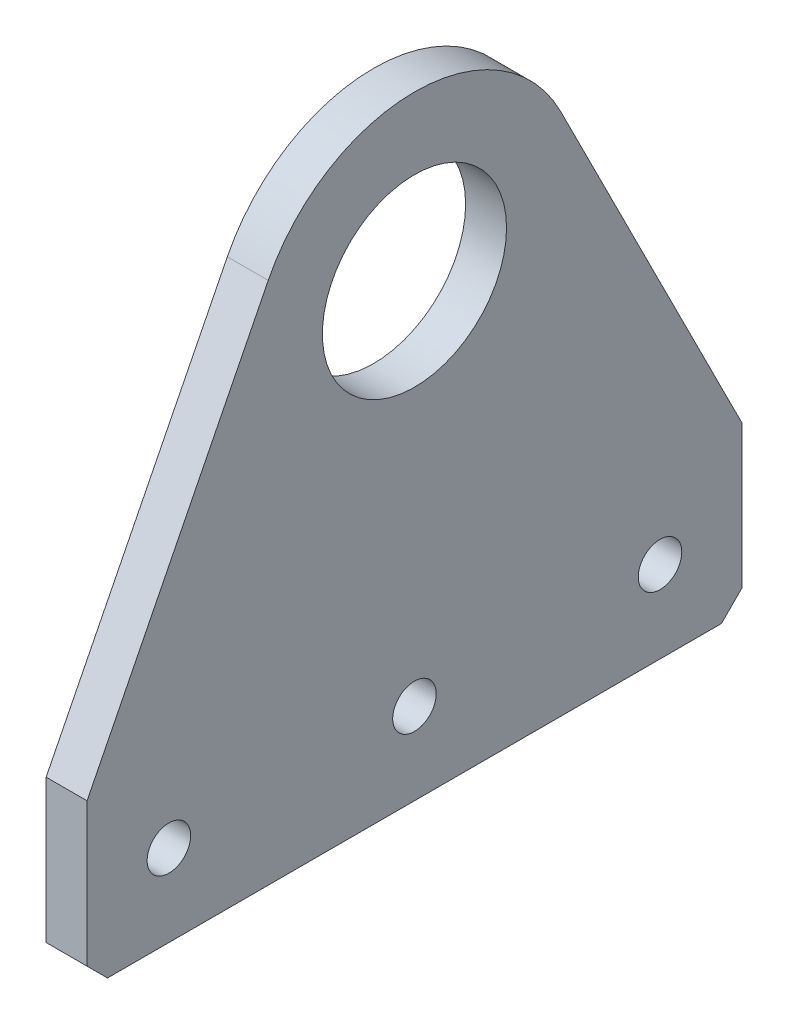
SolidWorks part; units mm, degrees
material "6061-T6 (SS)"
ref_plane "Front Plane" through (0, 0, 0) normal (0, 0, 1) x (1, 0, 0)
ref_plane "Top Plane" through (0, 0, 0) normal (0, 1, 0) x (1, 0, 0)
ref_plane "Right Plane" through (0, 0, 0) normal (1, 0, 0) x (0, 0, -1)
sketch "Sketch1" plane through (0, 0, 0) normal (1, 0, 0) x (0, 0, -1)
  line L0 (0, 0) -> (0, 25.4)
  line L1 (0, 25.4) -> (28.1104, 81.2667)
  line L2 (73.4896, 81.2667) -> (101.6, 25.4)
  line L3 (101.6, 25.4) -> (101.6, 0)
  line L4 (101.6, 0) -> (0, 0)
  arc A0 (28.1104, 81.2667) -> (73.4896, 81.2667) centre (50.8, 69.85) cw
  circle A1 centre (50.8, 69.85) radius 14.2875
  dimension "D3" = 28.575
  dimension "D4" = 25.4
  dimension "D5" = 69.85
  dimension "D1" = 101.6
  dimension "D2" = 25.4
extrude "Boss-Extrude1" add sketch "Sketch1" along normal blind 6.35
sketch "Sketch2" plane through (6.35, 0, 0) normal (1, 0, 0) x (0, 0, -1)
  line L0 (0, 25.4) -> (0, 0) construction
  line L1 (101.6, 0) -> (101.6, 25.4) construction
  line L2 (0, 0) -> (101.6, 0) construction
  line L3 (12.7, 12.7) -> (88.9, 12.7) construction
  circle A0 centre (12.7, 12.7) radius 3.3782
  circle A1 centre (50.8, 12.7) radius 3.3782
  circle A2 centre (88.9, 12.7) radius 3.3782
  dimension "D1" = 12.7
  dimension "D2" = 12.7
  dimension "D3" = 12.7
  dimension "D4" = 6.7564
extrude "Cut-Extrude1" cut sketch "Sketch2" against normal through all
chamfer "Chamfer1" distance 3.175 angle 45 2 edges at (3.175, 0, -101.6) (3.175, 0, 0)
sketch "Sketch3" plane through (0, 0, 0) normal (1, 0, 0) x (0, 0, -1)
  line L0 (-16.891, -20.066) -> (0, 0) construction
  line L1 (-16.891, -20.066) -> (118.491, -20.066)
  line L2 (-16.891, -20.066) -> (-16.891, 115.316)
  line L3 (-16.891, 115.316) -> (118.491, 115.316)
  line L4 (118.491, -20.066) -> (118.491, 115.316)
  line L5 (118.491, 115.316) -> (101.6, 95.25) construction
  line L6 (50.8, 95.25) -> (101.6, 95.25) construction
  line L7 (101.6, 95.25) -> (101.6, 25.4) construction
  arc A0 (73.4896, 81.2667) -> (28.1104, 81.2667) centre (50.8, 69.85) ccw construction
  dimension "D1" = 135.382
  dimension "D2" = 135.382
sketch "Sketch4" plane through (6.35, 0, 0) normal (1, 0, 0) x (0, 0, -1)
  line L0 (1.1039, -5) -> (100.4961, -5)
  line L1 (100.4961, -5) -> (106.6, 1.1039)
  line L2 (106.6, 1.1039) -> (106.6, 26.587)
  line L3 (106.6, 26.587) -> (77.9561, 83.5141)
  line L4 (23.6439, 83.5141) -> (-5, 26.587)
  line L5 (-5, 26.587) -> (-5, 1.1039)
  line L6 (-5, 1.1039) -> (1.1039, -5)
  line L7 (3.175, 0) -> (98.425, 0)
  line L8 (98.425, 0) -> (101.6, 3.175)
  line L9 (101.6, 3.175) -> (101.6, 25.4)
  line L10 (101.6, 25.4) -> (73.4896, 81.2667)
  line L11 (28.1104, 81.2667) -> (0, 25.4)
  line L12 (0, 25.4) -> (0, 3.175)
  line L13 (0, 3.175) -> (3.175, 0)
  line L14 (3.175, 0) -> (98.425, 0) construction
  line L15 (98.425, 0) -> (101.6, 3.175) construction
  line L16 (101.6, 3.175) -> (101.6, 25.4) construction
  line L17 (101.6, 25.4) -> (73.4896, 81.2667) construction
  line L18 (28.1104, 81.2667) -> (0, 25.4) construction
  line L19 (0, 25.4) -> (0, 3.175) construction
  line L20 (0, 3.175) -> (3.175, 0) construction
  arc A0 (77.9561, 83.5141) -> (23.6439, 83.5141) centre (50.8, 69.85) ccw
  arc A1 (73.4896, 81.2667) -> (28.1104, 81.2667) centre (50.8, 69.85) ccw
  arc A2 (73.4896, 81.2667) -> (28.1104, 81.2667) centre (50.8, 69.85) ccw construction
  dimension "D1" = 0
  dimension "D2" = 5
